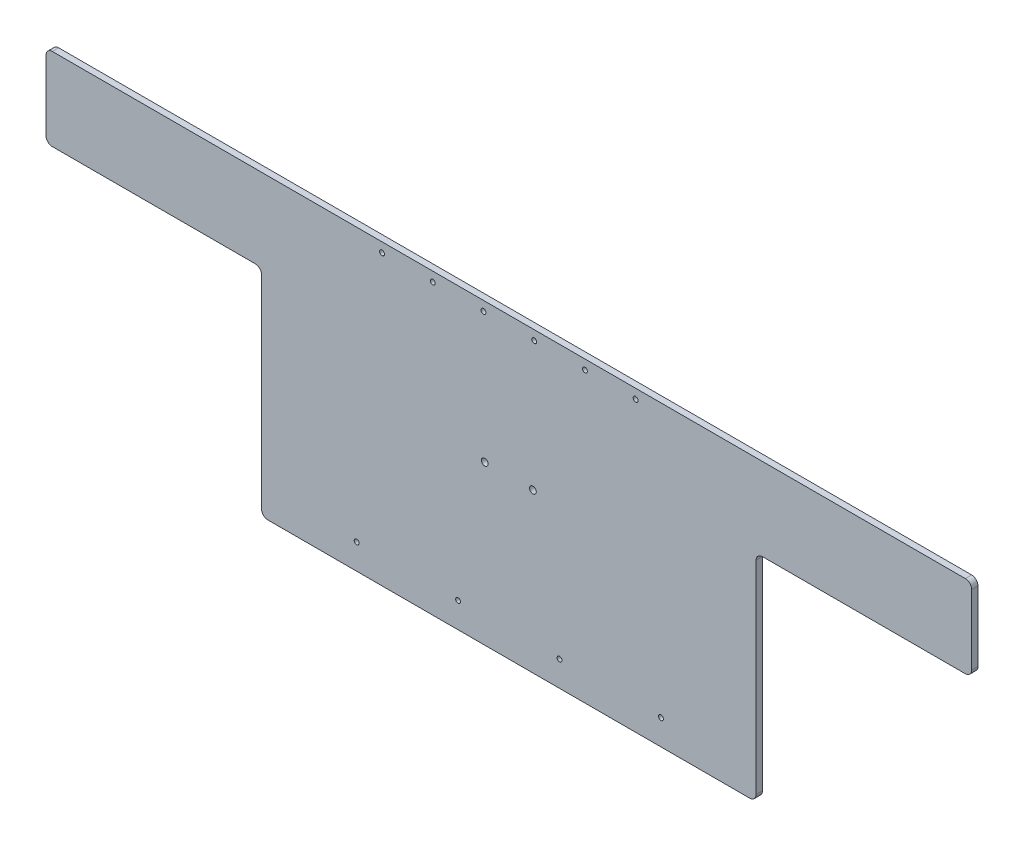
SolidWorks part; units mm, degrees
material "PC High Viscosity"
ref_plane "Front Plane" through (0, 0, 0) normal (0, 0, 1) x (1, 0, 0)
ref_plane "Top Plane" through (0, 0, 0) normal (0, 1, 0) x (1, 0, 0)
ref_plane "Right Plane" through (0, 0, 0) normal (1, 0, 0) x (0, 0, -1)
sketch "Sketch1" plane through (0, 0, 0) normal (0, 0, 1) x (1, 0, 0)
  line L0 (-463.55, -82.55) -> (-463.55, 0)
  line L1 (-463.55, 0) -> (463.55, 0)
  line L2 (463.55, 0) -> (463.55, -82.55)
  line L3 (463.55, -82.55) -> (247.65, -82.55)
  line L4 (247.65, -82.55) -> (247.65, -298.45)
  line L5 (247.65, -298.45) -> (-247.65, -298.45)
  line L6 (-247.65, -298.45) -> (-247.65, -82.55)
  line L7 (-247.65, -82.55) -> (-463.55, -82.55)
  point P9 (0, 0)
  dimension "D1" = 215.9
  dimension "D2" = 298.45
  dimension "D3" = 927.1
  dimension "D4" = 215.9
extrude "Boss-Extrude1" add sketch "Sketch1" along normal blind 6.35
sketch "Sketch2" plane through (0, 0, 6.35) normal (0, 0, 1) x (1, 0, 0)
  line L0 (463.55, 0) -> (-463.55, 0) construction
  circle A0 centre (127, -9.525) radius 2.4638
  dimension "D1" = 9.525
  dimension "D2" = 4.9276
  dimension "D3" = 127
extrude "Cut-Extrude1" cut sketch "Sketch2" against normal through all
pattern_linear "LPattern1" count 6 spacing 50.8 along (-1, 0, 0) of "Cut-Extrude1"
sketch "Sketch3" plane through (0, 0, 6.35) normal (0, 0, 1) x (1, 0, 0)
  line L1 (-247.65, -82.55) -> (-247.65, -298.45) construction
  line L2 (-247.65, -298.45) -> (247.65, -298.45) construction
  circle A0 centre (-152.4, -273.05) radius 2.4638
  dimension "D1" = 95.25
  dimension "D3" = 4.9276
  dimension "D2" = 25.4
extrude "Cut-Extrude2" cut sketch "Sketch3" against normal through all
pattern_linear "LPattern2" count 4 spacing 101.6 along (1, 0, 0) of "Cut-Extrude2"
sketch "Sketch4" plane through (0, 0, 6.35) normal (0, 0, 1) x (1, 0, 0)
  line L0 (463.55, 0) -> (-463.55, 0) construction
  circle A0 centre (-24.13, -139.7) radius 3.3655
  circle A1 centre (24.13, -139.7) radius 3.3655
  dimension "D1" = 24.13
  dimension "D4" = 6.731
  dimension "D2" = 24.13
  dimension "D3" = 139.7
extrude "Cut-Extrude3" cut sketch "Sketch4" against normal through all
fillet "Fillet1" radius 6.35 8 edges at (-463.55, 0, 3.175) (-463.55, -82.55, 3.175) (-247.65, -82.55, 3.175) (-247.65, -298.45, 3.175) (247.65, -298.45, 3.175) (463.55, 0, 3.175) (463.55, -82.55, 3.175) (247.65, -82.55, 3.175)
